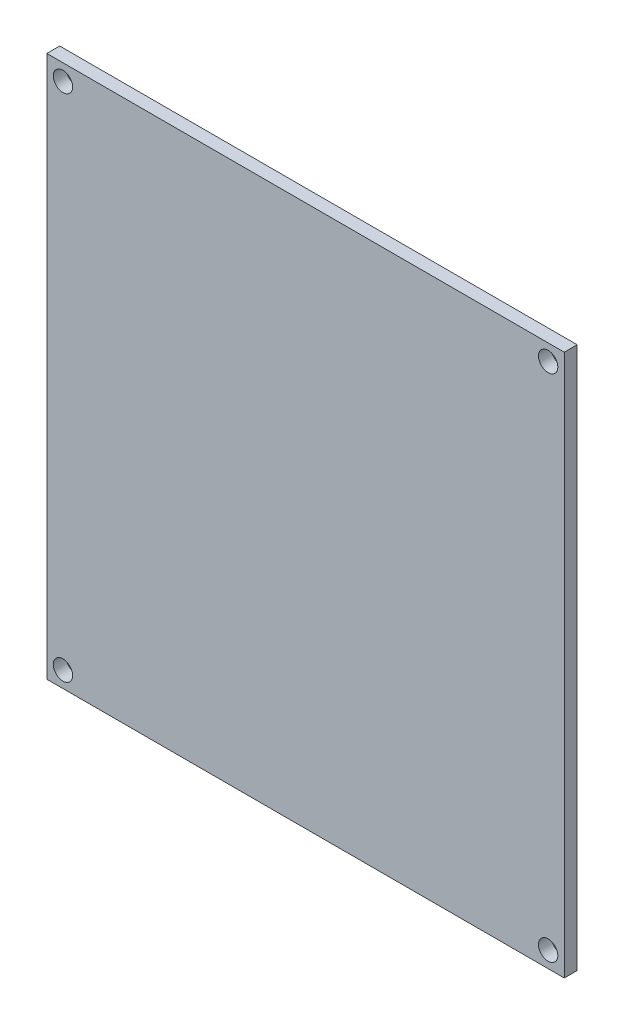
SolidWorks part; units mm, degrees
ref_plane "Front Plane" through (0, 0, 0) normal (0, 0, 1) x (1, 0, 0)
ref_plane "Top Plane" through (0, 0, 0) normal (0, 1, 0) x (1, 0, 0)
ref_plane "Right Plane" through (0, 0, 0) normal (1, 0, 0) x (0, 0, -1)
sketch "Sketch1" plane through (0, 0, 0) normal (0, 0, 1) x (1, 0, 0)
  line L1 (0, 0) -> (-80.2, 0)
  line L2 (0, 0) -> (0, -84)
  line L3 (0, -84) -> (-80.2, -84)
  line L4 (-80.2, 0) -> (-80.2, -84)
  dimension "D1" = 80.2
  dimension "D2" = 84
extrude "Boss-Extrude1" add sketch "Sketch1" along normal blind 2
sketch "Sketch2" plane through (0, 0, 2) normal (0, 0, 1) x (1, 0, 0)
  line L0 (-77.7, -2.5) -> (-2.5, -2.5) construction
  line L1 (-2.5, -2.5) -> (-2.5, -81.5) construction
  line L2 (-40.1, 0) -> (-40.1, -84) construction
  line L3 (-80.2, 0) -> (0, 0) construction
  line L4 (0, -84) -> (-80.2, -84) construction
  line L5 (0, -42) -> (-80.2, -42) construction
  line L6 (0, 0) -> (0, -84) construction
  line L7 (-80.2, -84) -> (-80.2, 0) construction
  line L8 (-2.5, -81.5) -> (-77.7, -81.5) construction
  line L9 (-77.7, -81.5) -> (-77.7, -2.5) construction
  line L11 (-80.2, 0) -> (-80.2, -84) construction
  line L12 (0, -84) -> (0, 0) construction
  line L13 (0, 0) -> (-80.2, 0) construction
  circle A0 centre (-77.7, -2.5) radius 1.5
  circle A1 centre (-2.5, -2.5) radius 1.5
  circle A2 centre (-77.7, -81.5) radius 1.5
  circle A3 centre (-2.5, -81.5) radius 1.5
  point P31 (0, 0)
  dimension "D3" = 3
  dimension "D1" = 2.5
  dimension "D2" = 2.5
  dimension "D4" = 2.5
extrude "Cut-Extrude1" cut sketch "Sketch2" against normal blind 42
